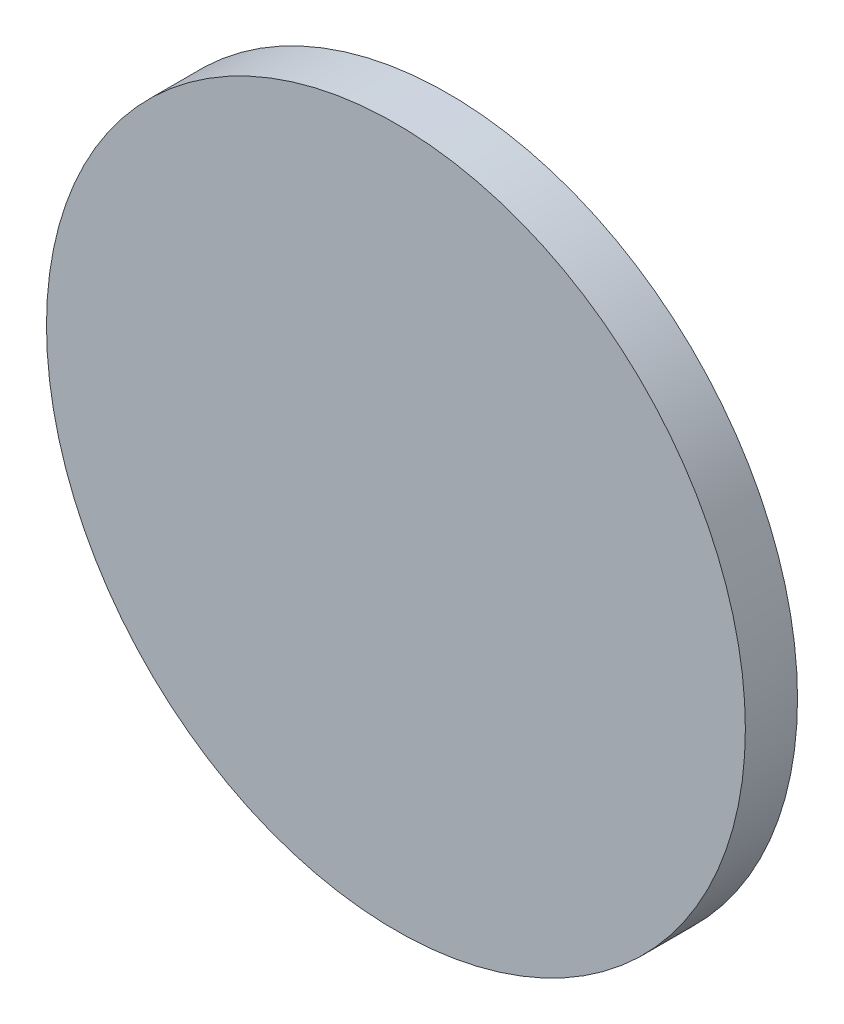
SolidWorks part; units mm, degrees
ref_plane "Front" through (0, 0, 0) normal (0, 0, 1) x (1, 0, 0)
ref_plane "Top" through (0, 0, 0) normal (0, 1, 0) x (1, 0, 0)
ref_plane "Right" through (0, 0, 0) normal (1, 0, 0) x (0, 0, -1)
sketch "Sketch1" plane through (0, 0, 0) normal (0, 0, 1) x (1, 0, 0)
  circle A0 centre (0, 0) radius 6.7
  dimension "D1" = 13.4
extrude "Boss-Extrude1" add sketch "Sketch1" along normal blind 1
